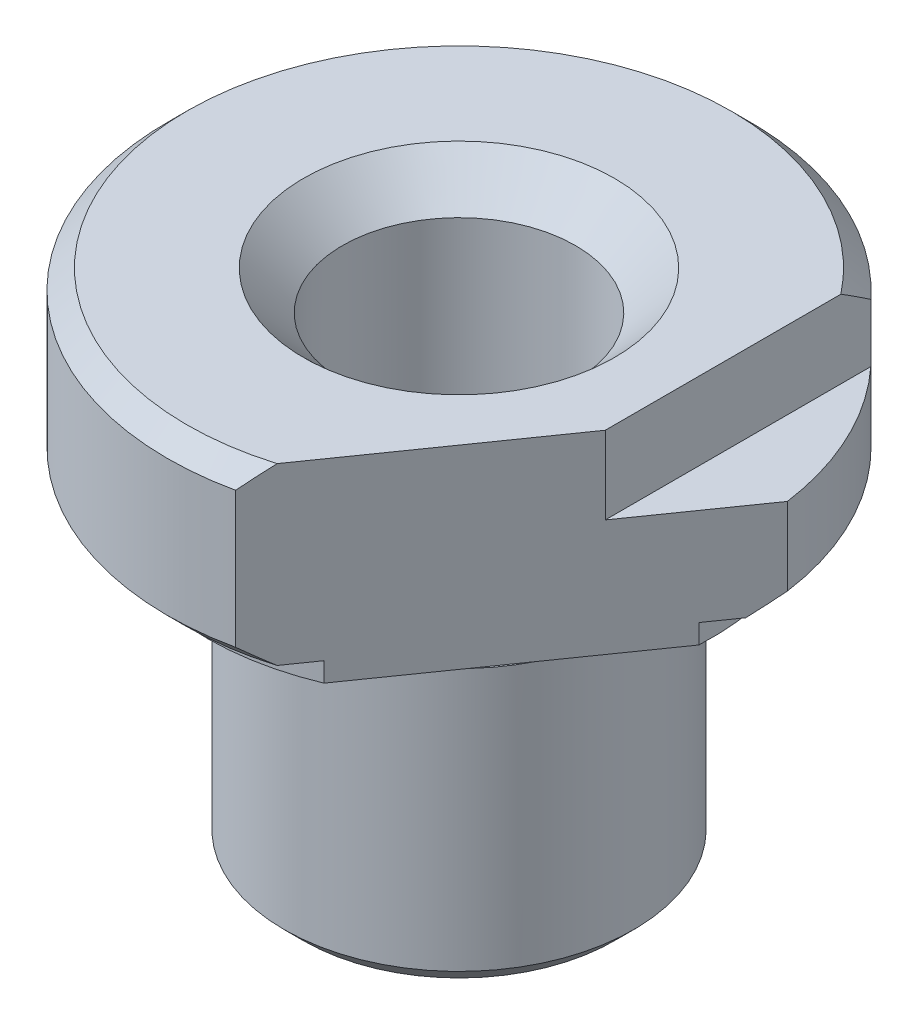
SolidWorks part; units mm, degrees
material "AISI 1020 钢，冷轧"
ref_plane "前视基准面" through (0, 0, 0) normal (0, 0, 1) x (1, 0, 0)
ref_plane "上视基准面" through (0, 0, 0) normal (0, 1, 0) x (1, 0, 0)
ref_plane "右视基准面" through (0, 0, 0) normal (1, 0, 0) x (0, 0, -1)
sketch "草图1" plane through (0, 0, 0) normal (0, 0, 1) x (1, 0, 0)
  line L0 (0, 0) -> (9, 0)
  line L1 (9, 0) -> (9, 15)
  line L2 (9, 15) -> (8, 15)
  line L3 (8, 15) -> (8, 16)
  line L4 (10, 16) -> (13, 16)
  line L5 (15, 17) -> (15, 26)
  line L6 (15, 26) -> (0, 26)
  line L7 (0, 26) -> (0, 0)
  line L8 (15, 17) -> (13, 17)
  line L9 (13, 17) -> (13, 16)
  line L10 (8, 16) -> (8, 16.5)
  line L11 (8, 16.5) -> (10, 16.5)
  line L12 (10, 16.5) -> (10, 16)
  dimension "D1" = 9
  dimension "D2" = 16
  dimension "D3" = 15
  dimension "D4" = 13
  dimension "D5" = 10
  dimension "D6" = 0.5
  dimension "D7" = 1
  dimension "D8" = 1
  dimension "D9" = 1
  dimension "D10" = 2
revolve "旋转1" add sketch "草图1" angle 360 about L7
sketch "草图2" plane through (0, 0, 0) normal (0, -1, 0) x (1, 0, 0)
  circle A0 centre (0, 0) radius 6
  dimension "D1" = 12
extrude "切除-拉伸1" cut sketch "草图2" against normal through all
sketch "草图3" plane through (0, 26, 0) normal (0, 1, 0) x (1, 0, 0)
  line L0 (11, 10.198) -> (11, -10.198)
  circle A0 centre (0, 0) radius 15 construction
  arc A1 (11, -10.198) -> (11, 10.198) centre (0, 0) ccw
  dimension "D1" = 11
extrude "切除-拉伸2" cut sketch "草图3" against normal blind 4
chamfer "倒角2" distance 2 angle 45 1 edges at (0, 26, -6)
chamfer "倒角3" distance 1 angle 45 3 edges at (0, 0, 9) (0, 17, 15) (-15, 26, 0)
chamfer "倒角4" distance 0.5 angle 45 2 edges at (0, 0, -6) (0, 15, 9)
sketch "草图4" plane through (0, 26, 0) normal (0, 1, 0) x (1, 0, 0)
  line L0 (3.1613, -14.6631) -> (14.86, 2.0444)
  line L1 (0, 0) -> (-17.9577, 0) construction
  arc A0 (11, 10.198) -> (11, -10.198) centre (0, 0) ccw construction
  arc A1 (11, -10.198) -> (11, 10.198) centre (0, 0) ccw construction
  arc A2 (11, -10.198) -> (14.86, 2.0444) centre (0, 0) ccw
  arc A3 (3.1613, -14.6631) -> (11, -10.198) centre (0, 0) ccw
  dimension "D1" = 55
  dimension "D2" = 11
extrude "切除-拉伸3" cut sketch "草图4" against normal blind 10
